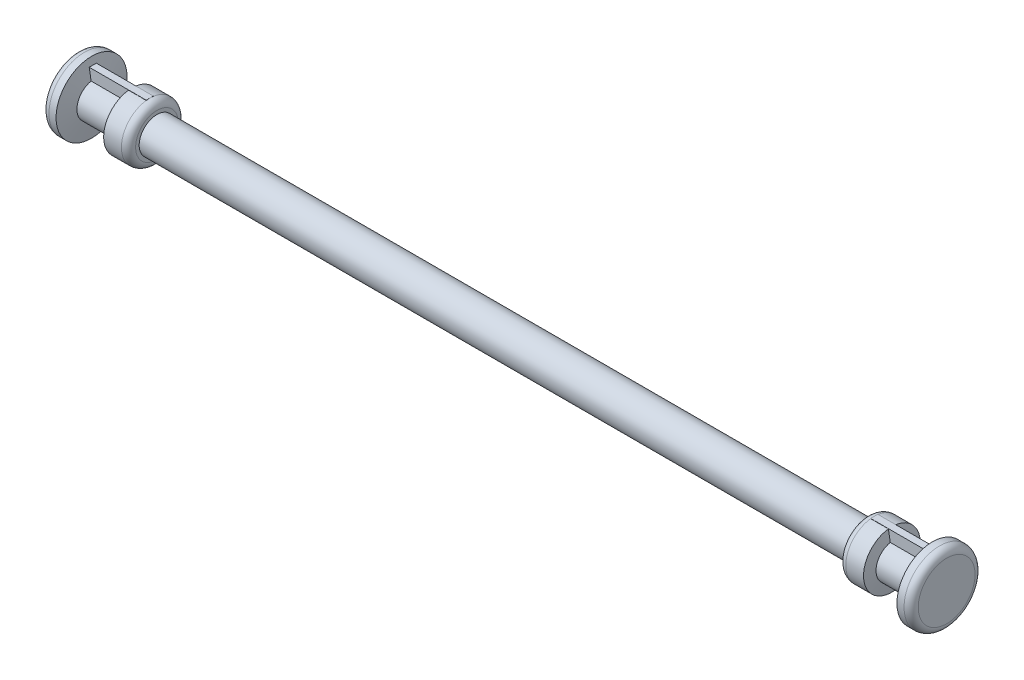
SolidWorks part; units mm, degrees
ref_plane "Front Plane" through (0, 0, 0) normal (0, 0, 1) x (1, 0, 0)
ref_plane "Top Plane" through (0, 0, 0) normal (0, 1, 0) x (1, 0, 0)
ref_plane "Right Plane" through (0, 0, 0) normal (1, 0, 0) x (0, 0, -1)
sketch "Sketch2" plane through (0, 0, 0) normal (0, 0, 1) x (1, 0, 0)
  line L0 (0, -5) -> (0, 32.8165) construction
  line L1 (100, 0) -> (-100, 0)
  line L2 (-100, 0) -> (-100, 3)
  line L3 (-100, 3) -> (-107, 3)
  line L4 (-107, 3) -> (-109.0977, -8.8965)
  line L5 (-107.529, 0) -> (-117.529, 0)
  line L6 (-117.529, 0) -> (-118.4106, 5)
  line L7 (-118.4106, 5) -> (-122.4106, 5)
  line L8 (-122.4106, 5) -> (-122.4106, -5)
  line L9 (-122.4106, -5) -> (122.4106, -5)
  line L10 (122.4106, 5) -> (122.4106, -5)
  line L11 (118.4106, 5) -> (122.4106, 5)
  line L12 (117.529, 0) -> (118.4106, 5)
  line L13 (107.529, 0) -> (117.529, 0)
  line L14 (107, 3) -> (109.0977, -8.8965)
  line L15 (100, 0) -> (100, 3)
  line L16 (100, 3) -> (107, 3)
  point P22 (0, 0)
  dimension "D1" = 100
  dimension "D2" = 7
  dimension "D3" = 80
  dimension "D4" = 10
  dimension "D5" = 100
  dimension "D6" = 4
  dimension "D7" = 5
  dimension "D8" = 8
  dimension "D9" = 10
revolve "Revolve2" add sketch "Sketch2" angle 360 about L9
sketch "Sketch3" plane through (122.4106, 0, 0) normal (1, 0, 0) x (0, 0, -1)
  line L0 (0, -5) -> (0, -1.1547) construction
  line L1 (1, -5.9552) -> (-1, -5.9552)
  line L2 (1, -5.9552) -> (1, 3)
  line L3 (1, 3) -> (-1, 3)
  line L4 (-1, -5.9552) -> (-1, 3)
  dimension "D1" = 2
  dimension "D2" = 1
  dimension "D3" = 8.9552
  dimension "D4" = 8
extrude "Boss-Extrude1" add sketch "Sketch3" against normal blind 20
sketch "Sketch4" plane through (-122.4106, 0, 0) normal (-1, 0, 0) x (0, 0, 1)
  line L0 (0, -6.0446) -> (0, 9.4157) construction
  line L1 (0, -5) -> (2, -5) construction
  line L3 (-1, 3) -> (1, 3)
  line L4 (-1, 3) -> (-1, -5)
  line L5 (-1, -5) -> (1, -5)
  line L6 (1, 3) -> (1, -5)
  dimension "D1" = 8
  dimension "D2" = 15.4604
  dimension "D3" = 1
  dimension "D4" = 1
extrude "Boss-Extrude2" add sketch "Sketch4" against normal blind 19
fillet "Fillet1" radius 2 4 edges at (122.4106, -5, 10) (100, -5, 8) (-100, -5, 8) (-122.4106, -5, 10)
sketch "Sketch6" plane through (0, 3, 0) normal (0, 1, 0) x (1, 0, 0)
  line L0 (-102, -8) -> (-102, 8) construction
  line L1 (-103.4106, 1) -> (-102, 1)
  line L2 (-103.4106, 1) -> (-103.4106, -1.0208)
  line L3 (-103.4106, -1.0208) -> (-102, -1.0208)
  line L4 (-102, 1) -> (-102, -1.0208)
extrude "Boss-Extrude4" add sketch "Sketch6" against normal up to surface
sketch "Sketch7" plane through (0, 3, 0) normal (0, 1, 0) x (1, 0, 0)
  line L0 (102, -8) -> (102, 8) construction
  line L1 (102.4106, 1) -> (102, 1)
  line L2 (102.4106, 1) -> (102.4106, -1.0035)
  line L3 (102.4106, -1.0035) -> (102, -1.0035)
  line L4 (102, 1) -> (102, -1.0035)
extrude "Boss-Extrude5" add sketch "Sketch7" against normal up to surface
